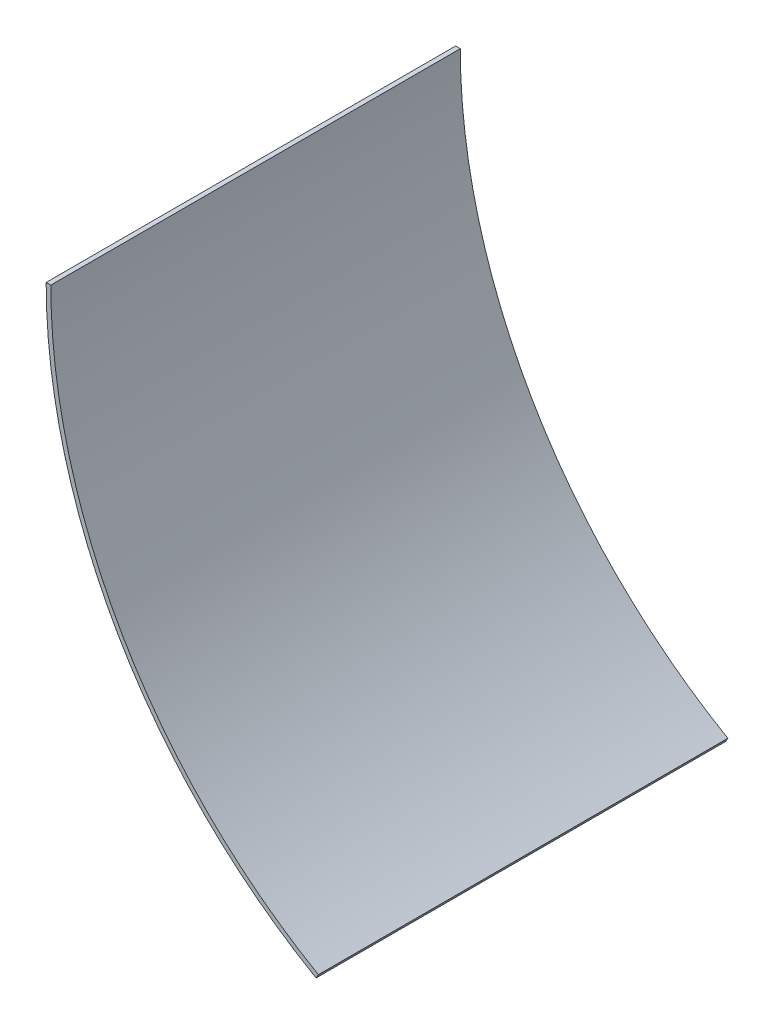
SolidWorks part; units mm, degrees
material "6061-T6 (SS)"
ref_plane "Front Plane" through (0, 0, 0) normal (0, 0, 1) x (1, 0, 0)
ref_plane "Top Plane" through (0, 0, 0) normal (0, 1, 0) x (1, 0, 0)
ref_plane "Right Plane" through (0, 0, 0) normal (1, 0, 0) x (0, 0, -1)
sketch "Sketch1" plane through (0, 0, 0) normal (0, 0, 1) x (1, 0, 0)
  line L0 (-182.5625, 0) -> (0, 0) construction
  line L1 (0, 0) -> (-91.2813, -158.1038) construction
  line L2 (-184.15, 0) -> (-182.5625, 0)
  line L3 (-91.2813, -158.1038) -> (-92.075, -159.4786)
  arc A0 (-182.5625, 0) -> (-91.2813, -158.1038) centre (0, 0) ccw
  arc A1 (-184.15, 0) -> (-92.075, -159.4786) centre (0, 0) ccw
  dimension "D1" = 182.5625
  dimension "D3" = 1.5875
  dimension "D2" = 60
extrude "Boss-Extrude1" add sketch "Sketch1" along normal blind 139.7
sketch "Bend-Lines3" [suppressed] plane through (0, 0, 0) normal (0, 1, 0) x (1, 0, 0)
sketch "Bounding-Box3" [suppressed] plane through (0, 0, 0) normal (0, 1, 0) x (1, 0, 0)
